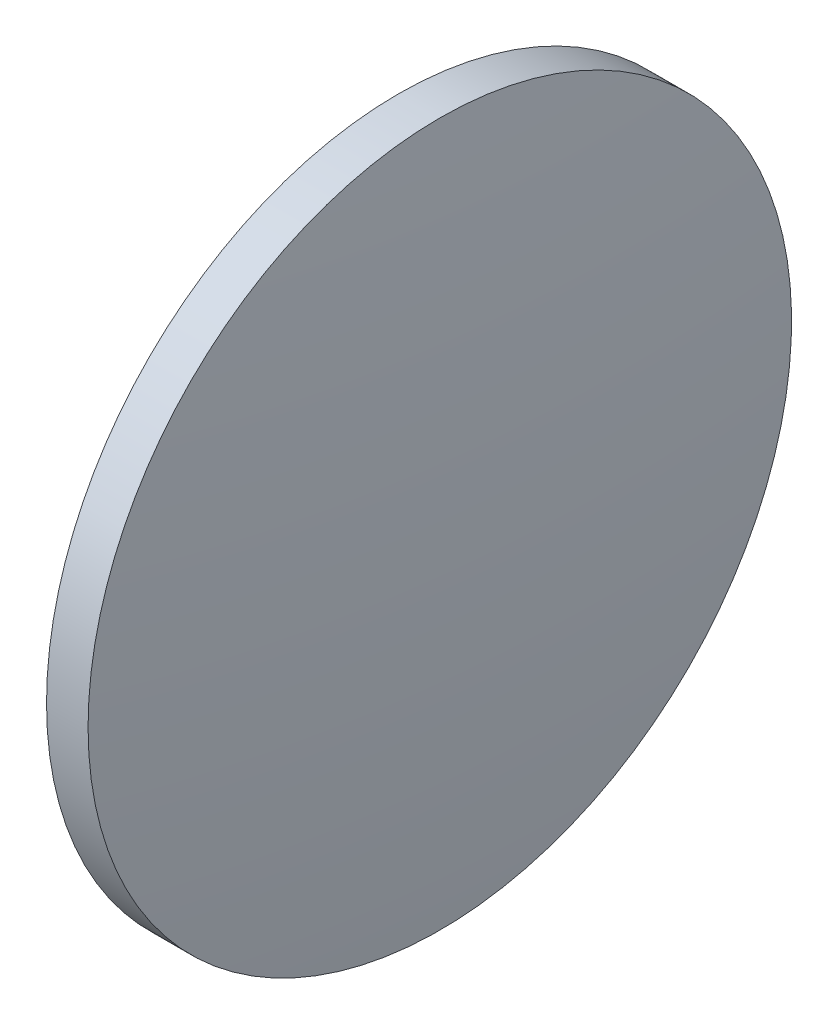
SolidWorks part; units mm, degrees
ref_plane "前视基准面" through (0, 0, 0) normal (0, 0, 1) x (1, 0, 0)
ref_plane "上视基准面" through (0, 0, 0) normal (0, 1, 0) x (1, 0, 0)
ref_plane "右视基准面" through (0, 0, 0) normal (1, 0, 0) x (0, 0, -1)
sketch "草图1" plane through (0, 0, 0) normal (0, 0, 1) x (1, 0, 0)
  line L0 (165.7441, 97.2322) -> (179.7312, 97.2322) construction
  line L1 (171.4164, 122.6322) -> (174.4164, 122.6322)
  line L2 (174.4164, 122.6322) -> (174.4164, 71.8322)
  line L3 (174.4164, 71.8322) -> (171.4164, 71.8322)
  line L4 (171.4164, 71.8322) -> (171.4164, 122.6322)
  arc A0 (171.4164, 122.6322) -> (171.4164, 71.8322) centre (439.6401, 97.2322) ccw
  arc A1 (174.4164, 71.8322) -> (174.4164, 122.6322) centre (-93.8074, 97.2322) ccw
  dimension "D1" = 50.8
  dimension "D2" = 3
revolve "旋转1" add sketch "草图1" angle 360 about L0
